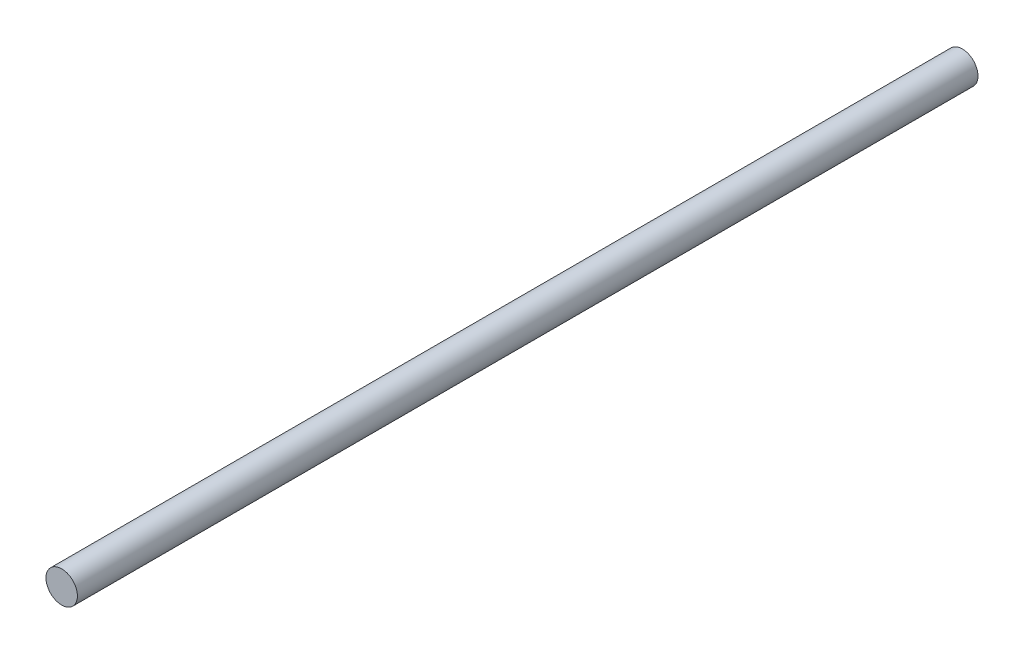
SolidWorks part; units mm, degrees
ref_plane "Спереди" through (0, 0, 0) normal (0, 0, 1) x (1, 0, 0)
ref_plane "Сверху" through (0, 0, 0) normal (0, 1, 0) x (1, 0, 0)
ref_plane "Справа" through (0, 0, 0) normal (1, 0, 0) x (0, 0, -1)
sketch "Эскиз1" plane through (0, 0, 0) normal (0, 0, 1) x (1, 0, 0)
  circle A0 centre (0, 0) radius 1.5
  dimension "D1" = 3
extrude "Бобышка-Вытянуть1" add sketch "Эскиз1" along normal blind 86
